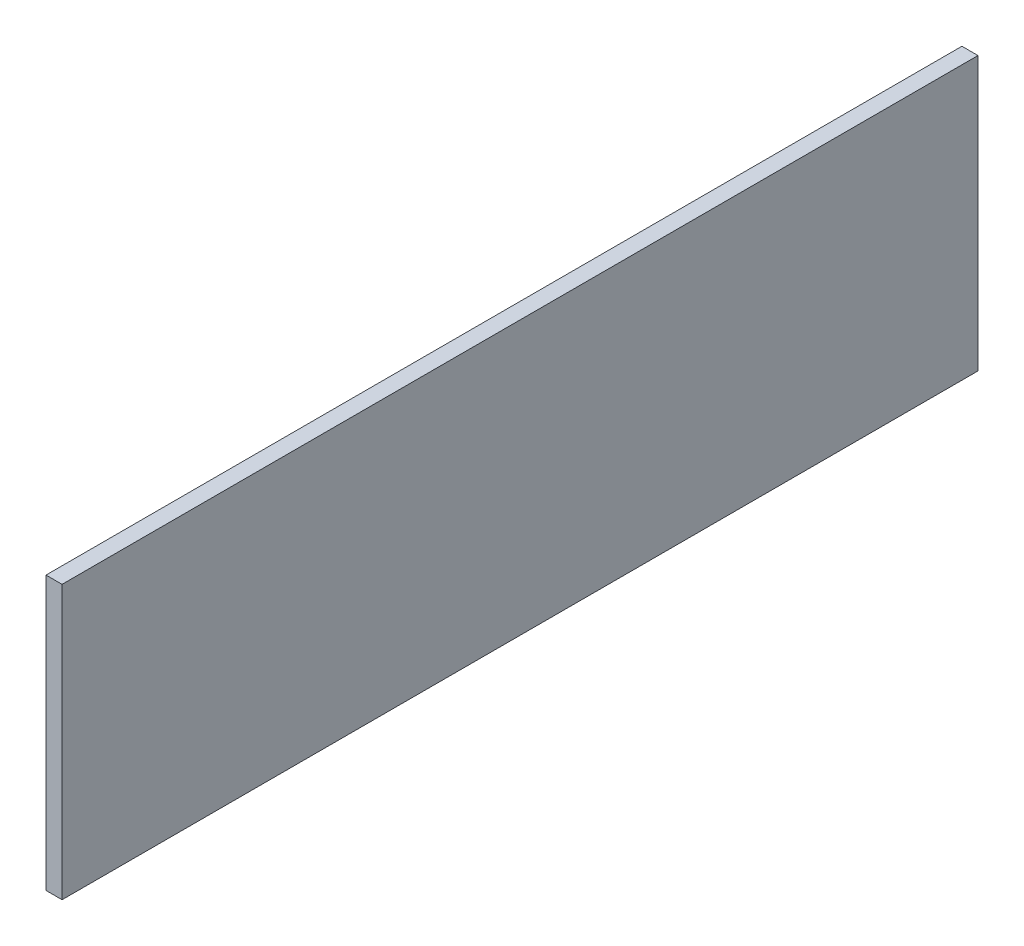
SolidWorks part; units mm, degrees
ref_plane "Front Plane" through (0, 0, 0) normal (0, 0, 1) x (1, 0, 0)
ref_plane "Top Plane" through (0, 0, 0) normal (0, 1, 0) x (1, 0, 0)
ref_plane "Right Plane" through (0, 0, 0) normal (1, 0, 0) x (0, 0, -1)
sketch "Sketch1" plane through (0, 0, 0) normal (1, 0, 0) x (0, 0, -1)
  line L1 (0, 0) -> (144.78, 0)
  line L2 (0, 0) -> (0, 43.18)
  line L3 (0, 43.18) -> (144.78, 43.18)
  line L4 (144.78, 0) -> (144.78, 43.18)
  dimension "D1" = 144.78
  dimension "D2" = 43.18
extrude "Boss-Extrude1" add sketch "Sketch1" along normal blind 2.54
